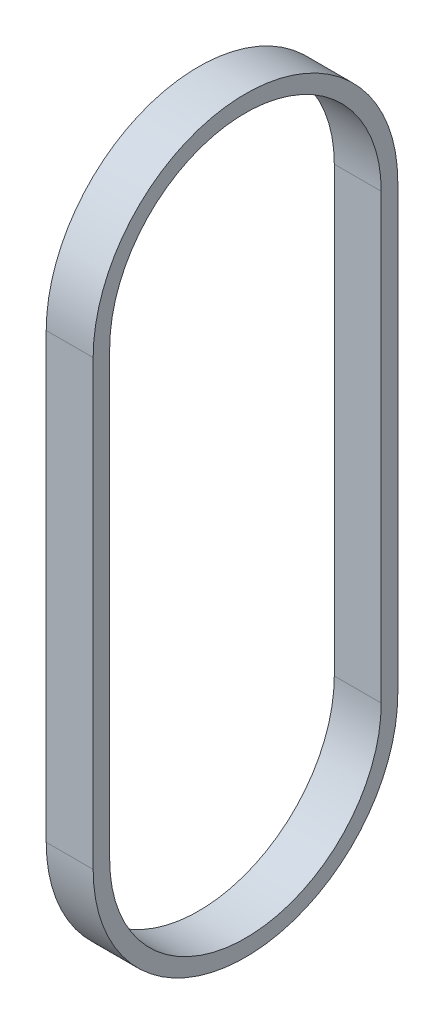
SolidWorks part; units mm, degrees
material "NEOPRENE"
ref_plane "Front Plane" through (0, 0, 0) normal (0, 0, 1) x (1, 0, 0)
ref_plane "Top Plane" through (0, 0, 0) normal (0, 1, 0) x (1, 0, 0)
ref_plane "Right Plane" through (0, 0, 0) normal (1, 0, 0) x (0, 0, -1)
sketch "Sketch1" plane through (0, 0, 0) normal (1, 0, 0) x (0, 0, -1)
  line L0 (-29.21, 85.0011) -> (-29.21, 0)
  line L1 (29.21, 85.0011) -> (29.21, 0)
  line L2 (26.035, 85.0011) -> (26.035, 0)
  line L3 (-26.035, 85.0011) -> (-26.035, 0)
  arc A0 (-29.21, 0) -> (29.21, 0) centre (0, 0) ccw
  arc A1 (-29.21, 85.0011) -> (29.21, 85.0011) centre (0, 85.0011) cw
  arc A2 (-26.035, 85.0011) -> (26.035, 85.0011) centre (0, 85.0011) cw
  arc A3 (-26.035, 0) -> (26.035, 0) centre (0, 0) ccw
  dimension "D1" = 29.21
  dimension "D2" = 85.0011
  dimension "D3" = 3.175
extrude "Boss-Extrude1" add sketch "Sketch1" along normal blind 9
